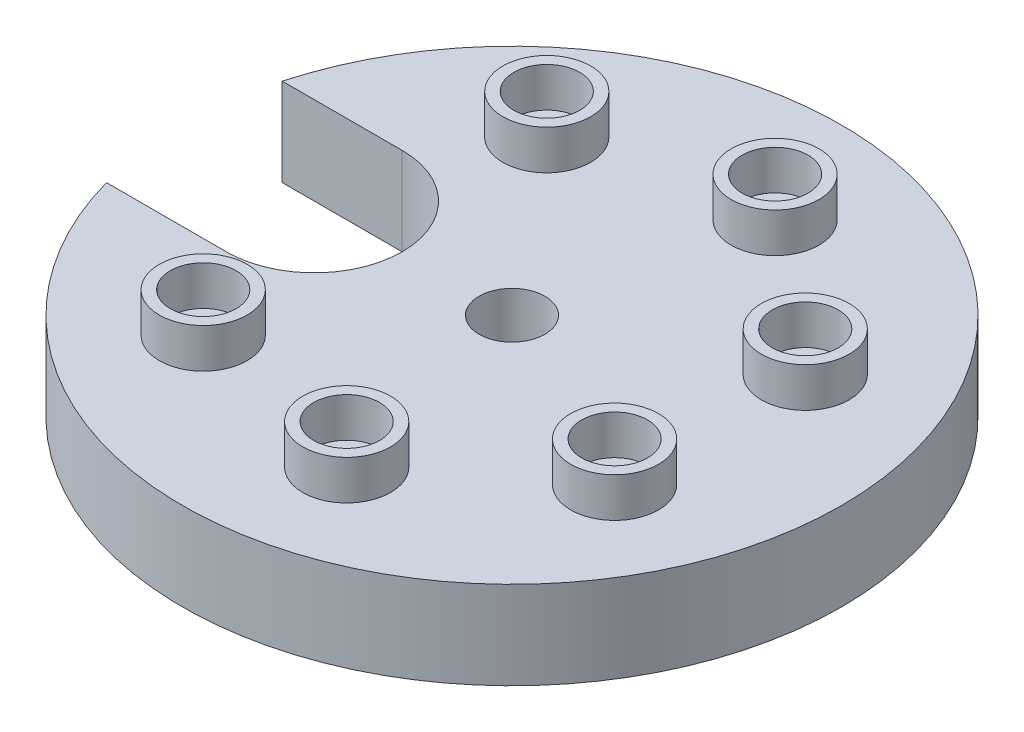
SolidWorks part; units mm, degrees
ref_plane "Front Plane" through (0, 0, 0) normal (0, 0, 1) x (1, 0, 0)
ref_plane "Top Plane" through (0, 0, 0) normal (0, 1, 0) x (1, 0, 0)
ref_plane "Right Plane" through (0, 0, 0) normal (1, 0, 0) x (0, 0, -1)
sketch "Sketch1" plane through (0, 0, 0) normal (0, 1, 0) x (1, 0, 0)
  circle A0 centre (0, 0) radius 75
  dimension "D1" = 150
extrude "Boss-Extrude1" add sketch "Sketch1" along normal blind 20
sketch "Sketch2" plane through (0, 20, 0) normal (0, 1, 0) x (1, 0, 0)
  circle A0 centre (-50, 0) radius 10
  circle A1 centre (0, 0) radius 50 construction
  circle A2 centre (-31.1745, 39.0916) radius 10
  circle A3 centre (11.126, 48.7464) radius 10
  circle A4 centre (45.0484, 21.6942) radius 10
  circle A5 centre (45.0484, -21.6942) radius 10
  circle A6 centre (11.126, -48.7464) radius 10
  circle A7 centre (-31.1745, -39.0916) radius 10
  circle A8 centre (-50, 0) radius 7.5
  circle A9 centre (-31.1745, 39.0916) radius 7.5
  circle A10 centre (11.126, 48.7464) radius 7.5
  circle A11 centre (45.0484, 21.6942) radius 7.5
  circle A12 centre (45.0484, -21.6942) radius 7.5
  circle A13 centre (11.126, -48.7464) radius 7.5
  circle A14 centre (-31.1745, -39.0916) radius 7.5
  point P19 (0, 0)
  point P33 (0, 0)
  dimension "D1" = 20
  dimension "D2" = 100
  dimension "D4" = 15
  dimension "D3" = 7
  dimension "D5" = 7
extrude "Boss-Extrude2" add sketch "Sketch2" along normal blind 9
sketch "Sketch3" plane through (0, 20, 0) normal (0, 1, 0) x (1, 0, 0)
  line L0 (0, 0) -> (-107.2312, 0) construction
  line L1 (-96.6404, 20) -> (-45, 20)
  line L2 (-96.6404, -20) -> (-45, -20)
  line L3 (-96.6404, 20) -> (-96.6404, -20)
  arc A0 (-45, 20) -> (-45, -20) centre (-45, 0) cw
  circle A1 centre (0, 0) radius 7.5
  dimension "D3" = 15
  dimension "D1" = 40
  dimension "D2" = 45
extrude "Cut-Extrude1" cut sketch "Sketch3" against normal blind 20
sketch "Sketch4" plane through (0, 0, 0) normal (0, 1, 0) x (1, 0, 0)
  circle A0 centre (-50, 0) radius 15.6219
extrude "Cut-Extrude2" cut sketch "Sketch4" along normal blind 60
